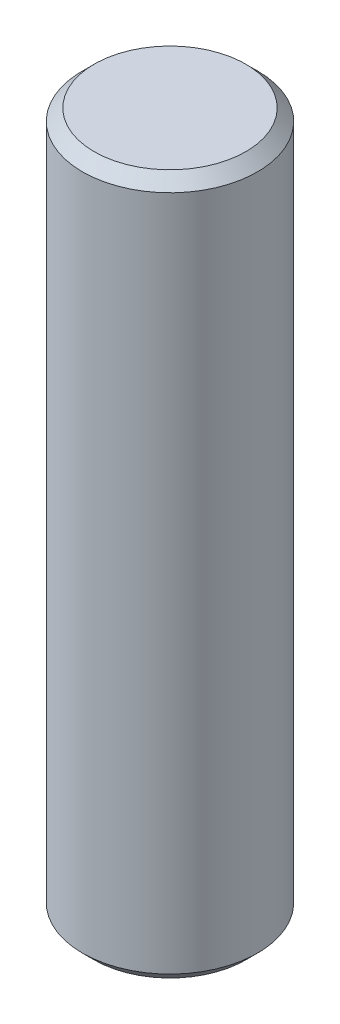
SolidWorks part; units mm, degrees
material "普通碳钢"
ref_plane "前视基准面" through (0, 0, 0) normal (0, 0, 1) x (1, 0, 0)
ref_plane "上视基准面" through (0, 0, 0) normal (0, 1, 0) x (1, 0, 0)
ref_plane "右视基准面" through (0, 0, 0) normal (1, 0, 0) x (0, 0, -1)
sketch "草图1" plane through (0, 0, 0) normal (0, 1, 0) x (1, 0, 0)
  circle A0 centre (0, 0) radius 1.5
  dimension "D1" = 3
extrude "凸台-拉伸1" add sketch "草图1" along normal blind 12
chamfer "倒角1" distance 0.2 angle 45 2 edges at (0, 12, 1.5) (0, 0, 1.5)
